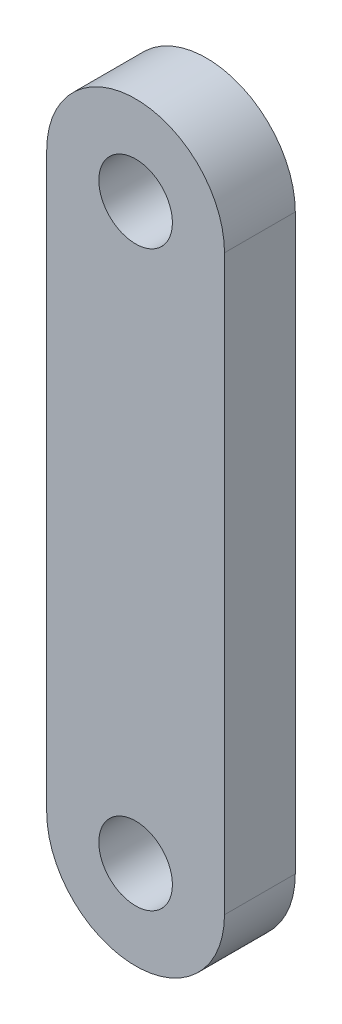
SolidWorks part; units mm, degrees
ref_plane "Front Plane" through (0, 0, 0) normal (0, 0, 1) x (1, 0, 0)
ref_plane "Top Plane" through (0, 0, 0) normal (0, 1, 0) x (1, 0, 0)
ref_plane "Right Plane" through (0, 0, 0) normal (1, 0, 0) x (0, 0, -1)
sketch "Sketch1" plane through (0, 0, 0) normal (0, 0, 1) x (1, 0, 0)
  line L0 (0, 38.075) -> (0, -13.36) construction
  line L1 (7.9756, 38.075) -> (7.9756, -13.36)
  line L2 (-7.9756, 38.075) -> (-7.9756, -13.36)
  arc A0 (7.9756, 38.075) -> (-7.9756, 38.075) centre (0, 38.075) ccw
  arc A1 (-7.9756, -13.36) -> (7.9756, -13.36) centre (0, -13.36) ccw
  circle A2 centre (0, 38.075) radius 3.302
  circle A3 centre (0, -13.36) radius 3.302
  point P3 (0, 12.3575)
  dimension "D1" = 6.604
  dimension "D2" = 6.604
  dimension "D3" = 51.435
  dimension "D4" = 15.9512
extrude "Boss-Extrude1" add sketch "Sketch1" along normal blind 6.35
